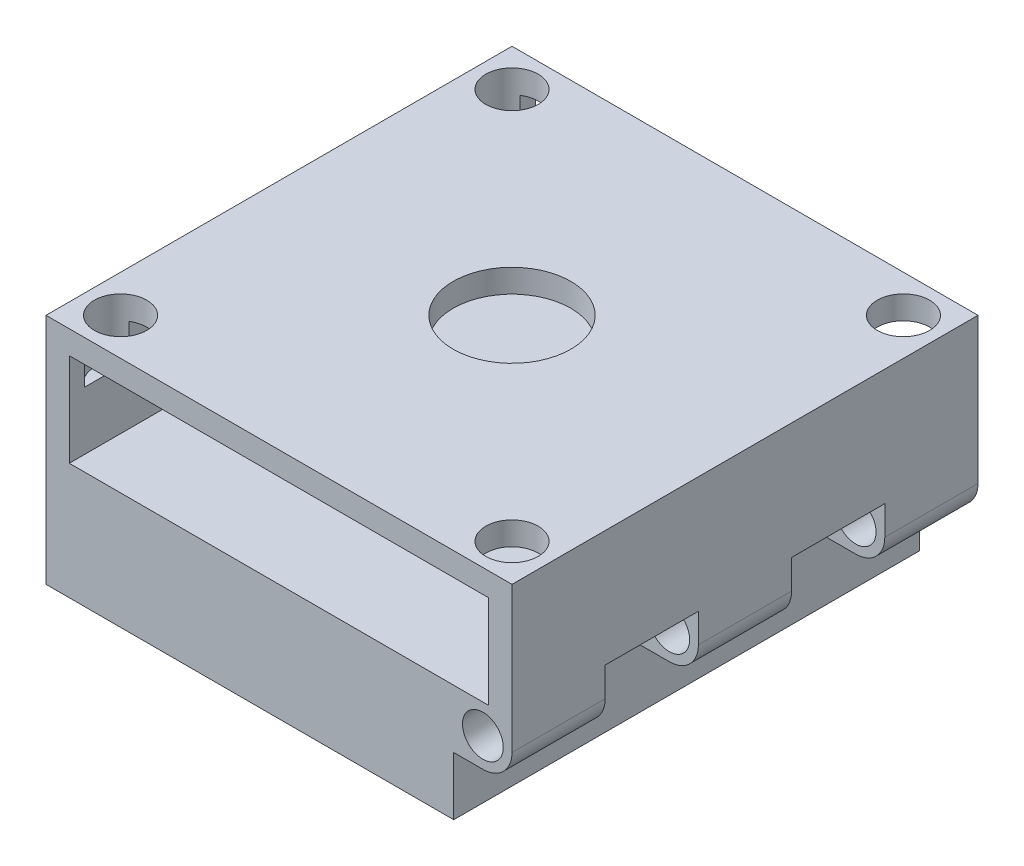
SolidWorks part; units mm, degrees
ref_plane "Front Plane" through (0, 0, 0) normal (0, 0, 1) x (1, 0, 0)
ref_plane "Top Plane" through (0, 0, 0) normal (0, 1, 0) x (1, 0, 0)
ref_plane "Right Plane" through (0, 0, 0) normal (1, 0, 0) x (0, 0, -1)
sketch "Sketch2" plane through (0, 0, 0) normal (0, 1, 0) x (1, 0, 0)
  line L1 (0, 0) -> (50.8, 0)
  line L2 (0, 0) -> (0, 50.8)
  line L3 (0, 50.8) -> (50.8, 50.8)
  line L4 (50.8, 0) -> (50.8, 50.8)
  dimension "D1" = 50.8
  dimension "D2" = 50.8
extrude "Boss-Extrude1" add sketch "Sketch2" along normal blind 19.05
shell "Shell1" thickness 2.54
sketch "Sketch4" plane through (0, 19.05, 0) normal (0, 1, 0) x (1, 0, 0)
  line L0 (0, 50.8) -> (0, 0) construction
  line L1 (50.8, 50.8) -> (0, 50.8) construction
  circle A0 centre (25.4, 25.4) radius 6.4135
  circle A1 centre (4.064, 46.736) radius 2.8575
  circle A2 centre (46.736, 46.736) radius 2.8575
  circle A3 centre (46.736, 4.064) radius 2.8575
  circle A4 centre (4.064, 4.064) radius 2.8575
  dimension "D3" = 12.827
  dimension "D4" = 5.715
  dimension "D1" = 25.4
  dimension "D2" = 25.4
  dimension "D5" = 4.064
  dimension "D6" = 4.064
  dimension "D7" = 4
extrude "Cut-Extrude1" cut sketch "Sketch4" against normal blind 6.35
sketch "Sketch5" plane through (0, 0, 0) normal (0, 0, 1) x (1, 0, 0)
  line L9 (50.8, 0) -> (44.45, 0)
  line L10 (50.8, 0) -> (50.8, 6.35)
  line L11 (50.8, 6.35) -> (44.45, 6.35)
  line L12 (44.45, 0) -> (44.45, 6.35)
  dimension "D1" = 6.35
extrude "Boss-Extrude3" add sketch "Sketch5" against normal up to surface (50.8 mm away) up to face at (25.4, 9.525, -50.8)
sketch "Sketch6" plane through (0, 0, 0) normal (0, 0, 1) x (1, 0, 0)
  line L0 (48.26, 6.35) -> (44.45, 6.35) construction
  line L1 (44.45, 6.35) -> (50.8, 6.35) construction
  line L2 (44.45, 6.35) -> (44.45, 0) construction
  line L3 (44.45, 0) -> (50.8, 0) construction
  line L4 (50.8, 6.35) -> (50.8, 0) construction
  line L5 (44.45, 6.35) -> (50.8, 0) construction
  line L6 (44.45, 0) -> (50.8, 6.35) construction
  line L7 (44.45, 6.35) -> (44.45, 2.54) construction
  circle A0 centre (47.625, 3.175) radius 2.2225
  dimension "D1" = 4.445
extrude "Cut-Extrude2" cut sketch "Sketch6" against normal through all
sketch "Sketch7" plane through (50.8, 0, 0) normal (1, 0, 0) x (0, 0, -1)
  line L1 (10.16, 0) -> (20.32, 0)
  line L2 (10.16, 0) -> (10.16, 6.35)
  line L3 (10.16, 6.35) -> (20.32, 6.35)
  line L4 (20.32, 0) -> (20.32, 6.35)
  line L16 (30.48, 0) -> (40.64, 0)
  line L17 (30.48, 0) -> (30.48, 6.35)
  line L18 (30.48, 6.35) -> (40.64, 6.35)
  line L19 (40.64, 0) -> (40.64, 6.35)
  line L20 (0, 0) -> (50.8, 0) construction
  line L23 (0, 19.05) -> (0, 0) construction
  dimension "D1" = 6.35
  dimension "D2" = 10.16
  dimension "D4" = 10.16
  dimension "D3" = 6.35
  dimension "D5" = 10.16
  dimension "D6" = 10.16
extrude "Cut-Extrude3" cut sketch "Sketch7" against normal blind 6.35
fillet "Fillet1" radius 3.175 3 edges at (50.8, 0, -45.72) (50.8, 0, -25.4) (50.8, 0, -5.08)
sketch "Sketch8" plane through (0, 2.54, 0) normal (0, 1, 0) x (1, 0, 0)
  circle A0 centre (25.4, 25.4) radius 6.4135
  circle A1 centre (25.4, 25.4) radius 6.4135 construction
extrude "Cut-Extrude4" cut sketch "Sketch8" against normal blind 6.35 contours A0
sketch "Sketch9" plane through (0, 0, 0) normal (0, -1, 0) x (1, 0, 0)
  line L1 (0, -50.8) -> (44.45, -50.8)
  line L2 (0, -50.8) -> (0, 0)
  line L3 (0, 0) -> (44.45, 0)
  line L4 (44.45, -50.8) -> (44.45, 0)
  circle A0 centre (25.4, -25.4) radius 6.4135
  circle A1 centre (25.4, -25.4) radius 6.4135 construction
extrude "Boss-Extrude4" add sketch "Sketch9" along normal blind 6.35 and the other way blind 6.35
